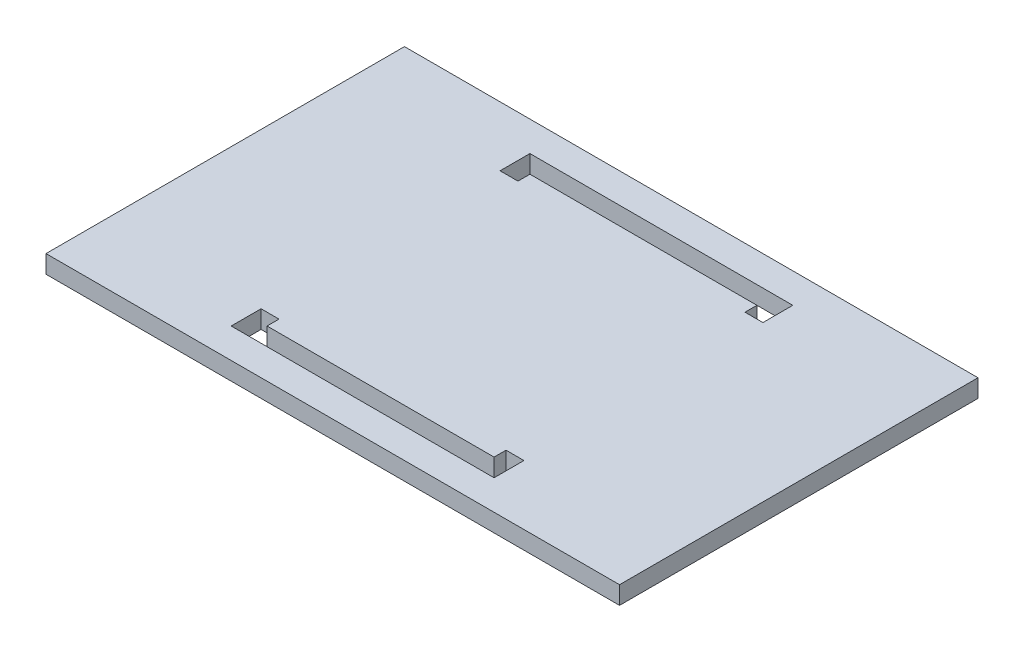
SolidWorks part; units mm, degrees
ref_plane "Front Plane" through (0, 0, 0) normal (0, 0, 1) x (1, 0, 0)
ref_plane "Top Plane" through (0, 0, 0) normal (0, 1, 0) x (1, 0, 0)
ref_plane "Right Plane" through (0, 0, 0) normal (1, 0, 0) x (0, 0, -1)
sketch "Sketch1" plane through (0, 0, 0) normal (0, 1, 0) x (1, 0, 0)
  line L0 (19, 22) -> (19, 20)
  line L1 (-19, 22) -> (19, 22)
  line L4 (19, 20) -> (22, 20)
  line L5 (22, 20) -> (22, 30)
  line L6 (22, 30) -> (48, 30)
  line L7 (48, 30) -> (48, -30)
  line L9 (-48, -30) -> (-48, 30)
  line L10 (-48, 30) -> (-22, 30)
  line L11 (-22, 30) -> (-22, 20)
  line L12 (-22, 20) -> (-19, 20)
  line L13 (-19, 20) -> (-19, 22)
  line L14 (48, -30) -> (22, -30)
  line L15 (22, -30) -> (22, -20)
  line L16 (22, -20) -> (19, -20)
  line L17 (19, -20) -> (19, -22)
  line L18 (19, -22) -> (-19, -22)
  line L19 (-19, -22) -> (-19, -20)
  line L20 (-19, -20) -> (-22, -20)
  line L21 (-22, -20) -> (-22, -30)
  line L22 (-22, -30) -> (-48, -30)
  line L24 (-22, 30) -> (22, 30)
  line L25 (-22, 30) -> (-22, 25)
  line L26 (-22, 25) -> (22, 25)
  line L27 (22, 30) -> (22, 25)
  line L28 (-22, -30) -> (22, -30)
  line L29 (-22, -30) -> (-22, -25)
  line L30 (-22, -25) -> (22, -25)
  line L31 (22, -30) -> (22, -25)
  point P0 (0, 22)
  point P23 (48, 0)
  dimension "D1" = 60
  dimension "D2" = 38
  dimension "D3" = 3
  dimension "D4" = 96
  dimension "D5" = 44
  dimension "D6" = 40
extrude "Boss-Extrude1" add sketch "Sketch1" along normal blind 3 contours L11 L26 L5 L24 | L30 L21 L28 L15 | L22 L21 L20 L19 L18 L17 L16 L15 L14 L7 L6 L5 L4 L0 L1 L13 L12 L11 L10 L9
